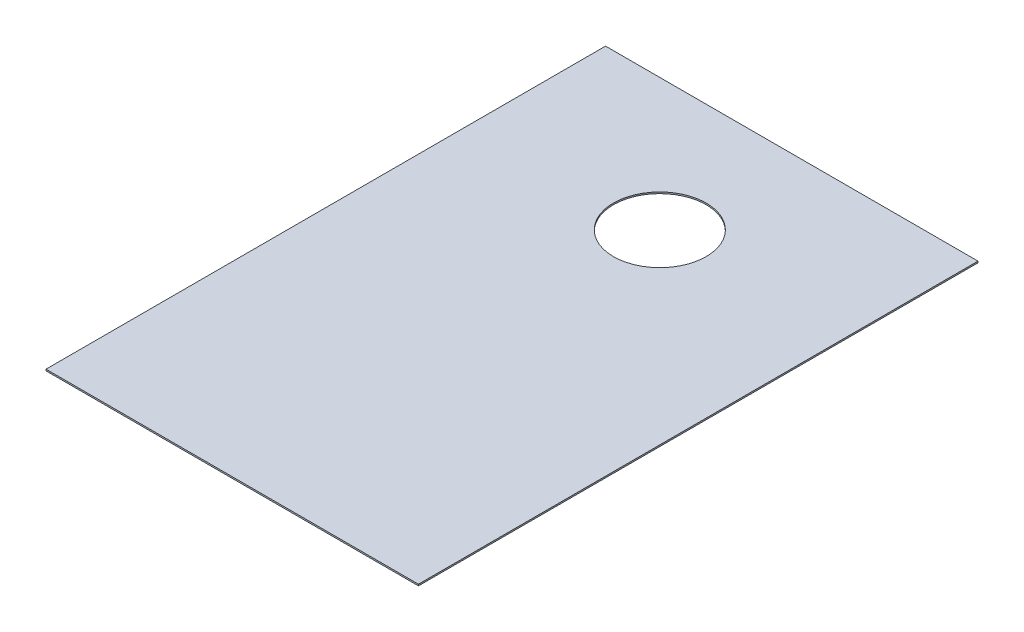
SolidWorks part; units mm, degrees
ref_plane "Front Plane" through (0, 0, 0) normal (0, 0, 1) x (1, 0, 0)
ref_plane "Top Plane" through (0, 0, 0) normal (0, 1, 0) x (1, 0, 0)
ref_plane "Right Plane" through (0, 0, 0) normal (1, 0, 0) x (0, 0, -1)
sketch "Sketch1" plane through (0, 0, 0) normal (0, 1, 0) x (1, 0, 0)
  line L1 (-6.35, 9.54) -> (6.35, 9.54)
  line L2 (-6.35, 9.54) -> (-6.35, -9.54)
  line L3 (-6.35, -9.54) -> (6.35, -9.54)
  line L4 (6.35, 9.54) -> (6.35, -9.54)
  line L5 (-6.35, 9.54) -> (6.35, -9.54) construction
  line L6 (-6.35, -9.54) -> (6.35, 9.54) construction
  point P0 (0, 0)
  dimension "D1" = 12.7
  dimension "D2" = 19.08
extrude "Boss-Extrude1" add sketch "Sketch1" along normal blind 0.051
sketch "Sketch2" plane through (0, 0.051, 0) normal (0, 1, 0) x (1, 0, 0)
  line L0 (0, -0.0281) -> (0, 0.0281) construction
  line L1 (6.35, 9.54) -> (-6.35, 9.54) construction
  circle A0 centre (0, 5.04) radius 1.5818
  point P2 (0, 0)
  dimension "D1" = 4.5
extrude "Cut-Extrude1" cut sketch "Sketch2" against normal through all
